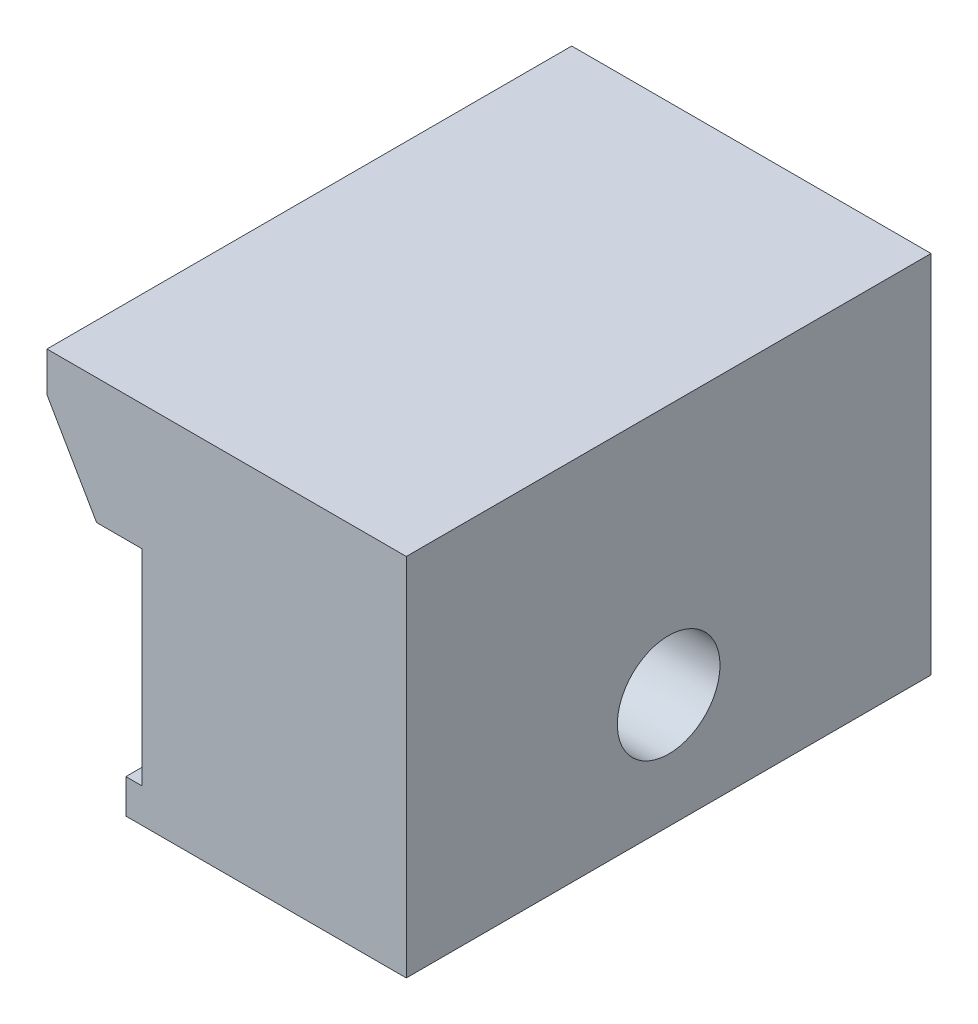
SolidWorks part; units mm, degrees
material "Сплав 2024"
ref_plane "Спереди" through (0, 0, 0) normal (0, 0, 1) x (1, 0, 0)
ref_plane "Сверху" through (0, 0, 0) normal (0, 1, 0) x (1, 0, 0)
ref_plane "Справа" through (0, 0, 0) normal (1, 0, 0) x (0, 0, -1)
sketch "Эскиз1" plane through (0, 0, 0) normal (0, 0, 1) x (1, 0, 0)
  line L1 (0, 0) -> (-12.29, 0)
  line L2 (-13.5746, 10.5) -> (-16.75, 16)
  line L3 (-16.75, 16) -> (0, 16)
  line L4 (0, 16) -> (0, 0)
  line L5 (-13.5746, 10.5) -> (-11.5746, 10.5)
  line L6 (-11.5746, 10.5) -> (-11.5746, 1.5)
  line L7 (-12.29, 0) -> (-12.29, 1.5)
  line L8 (-12.29, 1.5) -> (-11.5746, 1.5)
  dimension "D1" = 2
  dimension "D2" = 5.5
  dimension "D3" = 16.75
  dimension "D4" = 60
  dimension "D5" = 1.5
  dimension "D6" = 16
  dimension "D7" = 12.29
extrude "Бобышка-Вытянуть1" add sketch "Эскиз1" along normal blind 23
sketch "Эскиз2" plane through (-11.5746, 0, 0) normal (1, 0, 0) x (0, 0, -1)
  line L0 (-23, 5) -> (0, 5) construction
  line L1 (-23, 0) -> (-23, 16) construction
  line L2 (0, 0) -> (0, 16) construction
  line L3 (-23, 0) -> (0, 0) construction
  line L4 (-19, 0) -> (-19, 16) construction
  line L5 (-23, 16) -> (0, 16) construction
  line L6 (-4, 16) -> (-4, 0) construction
  line L7 (-11.5, 16) -> (-11.5, 0) construction
  circle A0 centre (-19, 5) radius 2.5
  circle A1 centre (-4, 5) radius 2.5
  dimension "D4" = 5
  dimension "D1" = 5
  dimension "D2" = 7.5
extrude "Вырез-Вытянуть1" cut sketch "Эскиз2" along normal blind 4 and the other way through all
hole_wizard "Отверстие с зазором M41" positions "Эскиз4" profile "Эскиз3" hole size "M4" standard "Din" end condition through all
sketch "Эскиз4" plane through (0, 1.5428, 4.5254) normal (-1, 0, 0) x (0, 0, 1)
  line L0 (18.4746, 3.4572) -> (-4.5254, 3.4572) construction
  line L1 (6.9746, 14.4572) -> (6.9746, -1.5428) construction
  point P0 (6.9746, 3.4572)
sketch "Эскиз3" plane through (0, 5, 11.5) normal (0, 1, 0) x (0, 0, -1)
  line L0 (0, 0) -> (0, 16.75)
  line L1 (0, 16.75) -> (2.25, 16.75)
  line L2 (2.25, 16.75) -> (2.25, 0)
  line L5 (2.25, 0) -> (0, 0)
  line L11 (0, -6.35) -> (0, 107.95) construction
  dimension "Диаметр сквозного отверстия" = 4.5
  dimension "Глубина сквозного отверстия" = 16.75
chamfer "Фаска1" distance 1 angle 90 1 edges at (-16.75, 16, 11.5)
